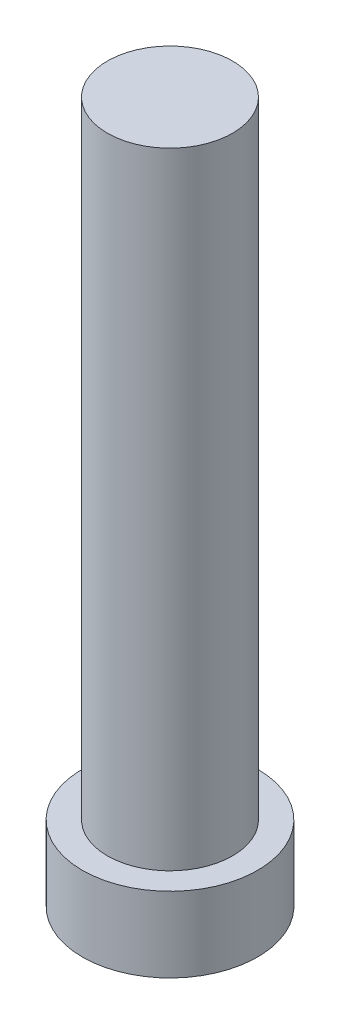
SolidWorks part; units mm, degrees
ref_plane "Front Plane" through (0, 0, 0) normal (0, 0, 1) x (1, 0, 0)
ref_plane "Top Plane" through (0, 0, 0) normal (0, 1, 0) x (1, 0, 0)
ref_plane "Right Plane" through (0, 0, 0) normal (1, 0, 0) x (0, 0, -1)
sketch "Sketch1" plane through (0, 0, 0) normal (0, 1, 0) x (1, 0, 0)
  circle A0 centre (0, 0) radius 3.5
  dimension "D1" = 7
extrude "Boss-Extrude1" add sketch "Sketch1" along normal blind 3
sketch "Sketch2" plane through (0, 3, 0) normal (0, 1, 0) x (1, 0, 0)
  circle A0 centre (0, 0) radius 2.5
  dimension "D1" = 5
extrude "Boss-Extrude2" add sketch "Sketch2" along normal blind 25
